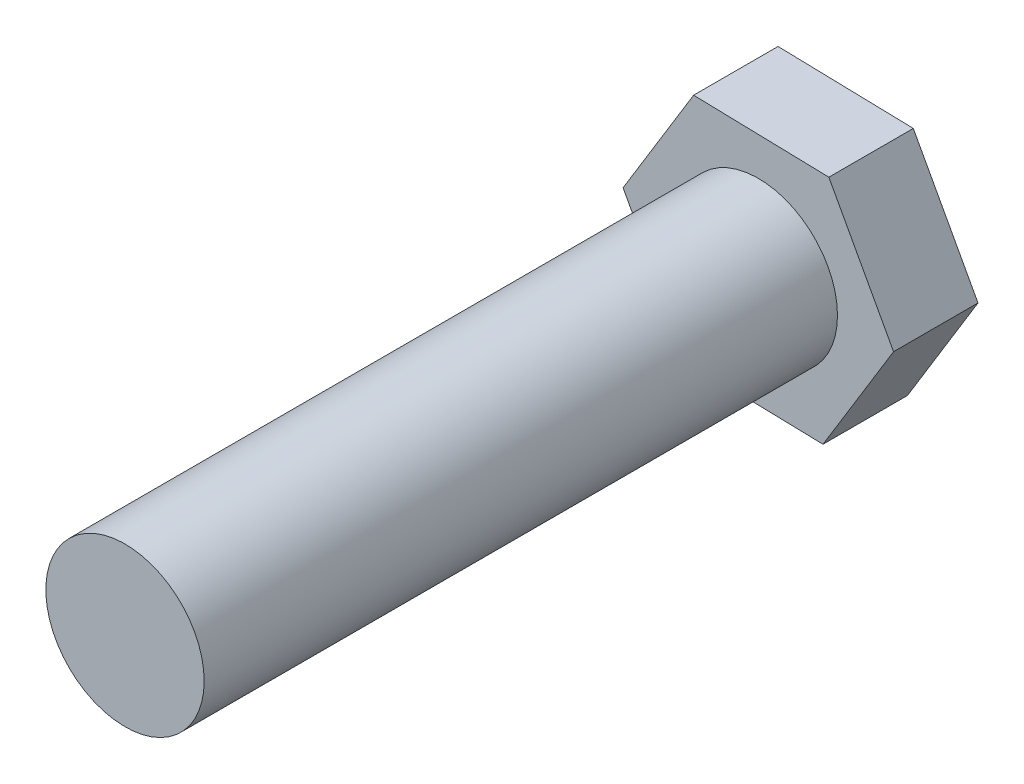
SolidWorks part; units mm, degrees
ref_plane "Front Plane" through (0, 0, 0) normal (0, 0, 1) x (1, 0, 0)
ref_plane "Top Plane" through (0, 0, 0) normal (0, 1, 0) x (1, 0, 0)
ref_plane "Right Plane" through (0, 0, 0) normal (1, 0, 0) x (0, 0, -1)
sketch "Sketch1" plane through (0, 0, 0) normal (0, 0, 1) x (1, 0, 0)
  line L1 (4.2443, 6.9446) -> (-3.892, 7.148)
  line L2 (-3.892, 7.148) -> (-8.1364, 0.2034)
  line L3 (-8.1364, 0.2034) -> (-4.2443, -6.9446)
  line L4 (-4.2443, -6.9446) -> (3.892, -7.148)
  line L5 (3.892, -7.148) -> (8.1364, -0.2034)
  line L6 (8.1364, -0.2034) -> (4.2443, 6.9446)
  circle A1 centre (0, 0) radius 7.0485 construction
extrude "Extrude1" add sketch "Sketch1" along normal blind 43.18
sketch "Sketch2" plane through (0, 0, 43.18) normal (0, 0, 1) x (1, 0, 0)
  circle A0 centre (0, 0) radius 4.7625
extrude "Extrude2" cut sketch "Sketch2" against normal blind 38.1 flip side to cut
